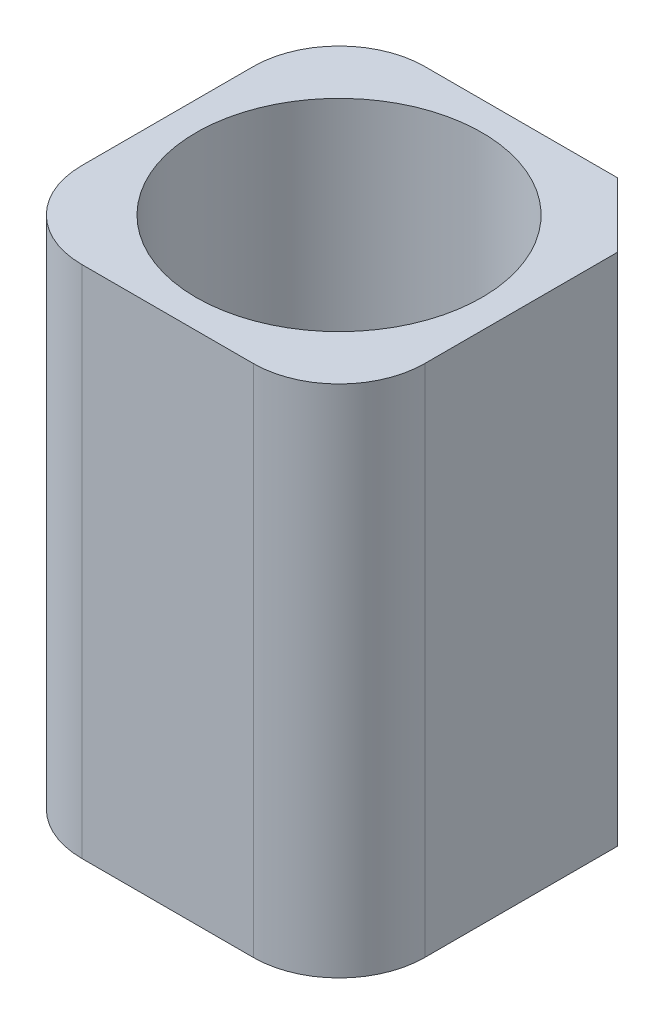
SolidWorks part; units mm, degrees
ref_plane "Front Plane" through (0, 0, 0) normal (0, 0, 1) x (1, 0, 0)
ref_plane "Top Plane" through (0, 0, 0) normal (0, 1, 0) x (1, 0, 0)
ref_plane "Right Plane" through (0, 0, 0) normal (1, 0, 0) x (0, 0, -1)
sketch "Sketch1" plane through (0, 0, 0) normal (0, 1, 0) x (1, 0, 0)
  line L0 (1.875, 3) -> (3, 1.875)
  line L1 (-3, -3) -> (3, -3)
  line L2 (-3, -3) -> (-3, 3)
  line L3 (-3, 3) -> (3, 3)
  line L4 (3, -3) -> (3, 3)
  line L5 (-3, -3) -> (3, 3) construction
  line L6 (-3, 3) -> (3, -3) construction
  circle A0 centre (-1.5, -1.5) radius 1.5
  circle A1 centre (-1.5, 1.5) radius 1.5
  circle A2 centre (1.5, -1.5) radius 1.5
  circle A3 centre (0, 0) radius 2.5
  point P0 (0, 0)
  dimension "D5" = 3
  dimension "D6" = 5
  dimension "D1" = 6
  dimension "D2" = 6
  dimension "D3" = 1.125
  dimension "D4" = 1.125
extrude "Boss-Extrude1" add sketch "Sketch1" along normal mid plane 9 contours A1 L2 A0 | A1 | A0 | A2 | A2 A0 L1 | A2 L4 L0 L3 A1 A0
sketch "Sketch2" plane through (0, -4.5, 0) normal (0, -1, 0) x (1, 0, 0)
  line L0 (-3, 1.5) -> (-3, -1.5) construction
  line L1 (-2.5, 1.75) -> (-2.225, 1.75)
  line L2 (-2.5, 1.75) -> (-2.5, 1.475)
  line L3 (-2.5, 1.475) -> (-2.225, 1.475)
  line L4 (-2.225, 1.75) -> (-2.225, 1.475)
  line L5 (-2.5, 1.75) -> (-2.225, 1.475) construction
  line L6 (-2.5, 1.475) -> (-2.225, 1.75) construction
  line L7 (-2.25, -2.225) -> (-1.975, -2.225)
  line L8 (-2.25, -2.225) -> (-2.25, -2.5)
  line L9 (-2.25, -2.5) -> (-1.975, -2.5)
  line L10 (-1.975, -2.225) -> (-1.975, -2.5)
  line L11 (-2.25, -2.225) -> (-1.975, -2.5) construction
  line L12 (-2.25, -2.5) -> (-1.975, -2.225) construction
  line L19 (-1.5, 3) -> (1.5, 3) construction
  line L20 (3, 1.5) -> (3, -1.875) construction
  line L21 (-1.5, -3) -> (1.875, -3) construction
  line L23 (1.98, -2.5) -> (1.705, -2.5)
  line L24 (1.98, -2.5) -> (1.98, -2.225)
  line L25 (1.98, -2.225) -> (1.705, -2.225)
  line L26 (1.705, -2.5) -> (1.705, -2.225)
  point P0 (-2.3625, 1.6125)
  point P5 (-2.1125, -2.3625)
  point P15 (-2.5, 1.6125)
  dimension "D1" = 0.5
  dimension "D2" = 0.275
  dimension "D3" = 0.275
  dimension "D5" = 1.25
  dimension "D6" = 0.5
  dimension "D7" = 0.75
  dimension "D8" = 0.5
  dimension "D9" = 1.02
  dimension "D10" = 0.275
extrude "Cut-Extrude1" cut sketch "Sketch2" against normal blind 1
